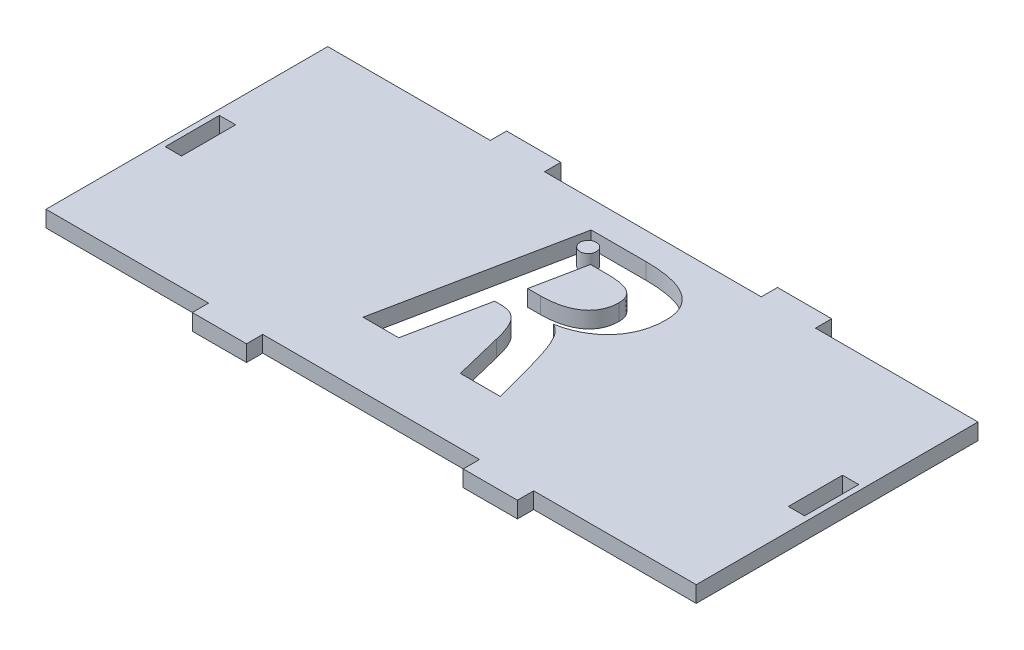
SolidWorks part; units mm, degrees
ref_plane "Front Plane" through (0, 0, 0) normal (0, 0, 1) x (1, 0, 0)
ref_plane "Top Plane" through (0, 0, 0) normal (0, 1, 0) x (1, 0, 0)
ref_plane "Right Plane" through (0, 0, 0) normal (1, 0, 0) x (0, 0, -1)
sketch "Sketch1" plane through (0, 0, 0) normal (0, 1, 0) x (1, 0, 0)
  line L0 (0, -42.4931) -> (0, 42.4931) construction
  line L1 (-26, 60) -> (26, 60)
  line L2 (-26, -60) -> (-26, -30)
  line L3 (-5, 56) -> (5, 59) construction
  line L4 (26, -60) -> (26, -30)
  line L7 (26, 20) -> (29, 30) construction
  line L8 (-26, 30) -> (-29, 30)
  line L9 (-26, -20) -> (-26, 20)
  line L10 (-26, 20) -> (-29, 20)
  line L11 (-29, 30) -> (-29, 20)
  line L12 (-26, 30) -> (-29, 20) construction
  line L13 (0, 0) -> (93.5777, 0) construction
  line L14 (-26, 20) -> (-29, 30) construction
  line L15 (26, 30) -> (29, 20) construction
  line L16 (29, 30) -> (29, 20)
  line L17 (26, 20) -> (29, 20)
  line L18 (26, -20) -> (26, 20)
  line L19 (26, 30) -> (29, 30)
  line L20 (26, -30) -> (29, -20) construction
  line L21 (-26, -20) -> (-29, -30) construction
  line L22 (-26, -30) -> (-29, -20) construction
  line L23 (26, -20) -> (29, -30) construction
  line L24 (26, -30) -> (29, -30)
  line L25 (-5, 59) -> (5, 56) construction
  line L26 (26, -20) -> (29, -20)
  line L27 (29, -30) -> (29, -20)
  line L28 (-29, -30) -> (-29, -20)
  line L29 (-26, -20) -> (-29, -20)
  line L30 (26, 30) -> (26, 60)
  line L31 (-26, -30) -> (-29, -30)
  line L32 (-26, 30) -> (-26, 60)
  line L33 (5, 59) -> (-5, 59)
  line L34 (5, 59) -> (5, 56)
  line L35 (-5, 56) -> (5, 56)
  line L36 (-5, 59) -> (-5, 56)
  line L39 (26, -60) -> (-26, -60)
  line L40 (5, -59) -> (-5, -59)
  line L46 (-5, -59) -> (-5, -56)
  line L47 (-5, -56) -> (5, -56)
  line L48 (5, -59) -> (5, -56)
  line L49 (-5, -59) -> (5, -56) construction
  line L50 (-5, -56) -> (5, -59) construction
  point P0 (0, 0)
  point P1 (-26, 0)
  point P2 (0, 0)
  point P3 (0, 60)
  point P10 (-27.5, 25)
  point P18 (27.5, 25)
  point P28 (27.5, -25)
  point P29 (-27.5, -25)
  point P34 (0, 57.5)
  point P35 (5, -57.5)
  point P40 (26, 0)
  point P44 (0, -57.5)
  point P46 (0, -60)
  dimension "D1" = 120
  dimension "D2" = 60
  dimension "D3" = 10
  dimension "D4" = 3
  dimension "D5" = 20
  dimension "D6" = 52
  dimension "D7" = 4
  dimension "D8" = 3
  dimension "D9" = 10
extrude "Boss-Extrude1" add sketch "Sketch1" along normal blind 3
move or copy body "Body-Move/Copy1" bodies to move or copy 101 copy no rotation origin (2.3358, 0, 2.3358) rotation axis (0, 1, 0) rotation angle 90
sketch "Sketch3" plane through (0, 3, 0) normal (0, 1, 0) x (1, 0, 0)
  line L0 (-20, -30.6716) -> (20, -30.6716) construction
  line L2 (-60, 21.3284) -> (-60, -30.6716) construction
  text T0 "R" font "Consolas" height 35
  point P7 (-60, -11.6063)
  point P10 (-60, -12.8013)
  dimension "D1" = 12
  dimension "D2" = 46
extrude "Cut-Extrude1" cut sketch "Sketch3" against normal blind 10
sketch "Sketch5" plane through (0, 3, 0) normal (0, 1, 0) x (1, 0, 0)
  line L0 (-6.3913, 16.3284) -> (3.7695, 16.3284) construction
  line L2 (-13.4928, -18.6716) -> (-6.3913, 16.3284) construction
  circle A0 centre (-3.9389, 13.3284) radius 1.5
  dimension "D1" = 3
  dimension "D2" = 3
  dimension "D3" = 3
extrude "Boss-Extrude2" add sketch "Sketch5" against normal up to surface (3 mm away) separate body up to face at (57.5, 0, 4.6716)
